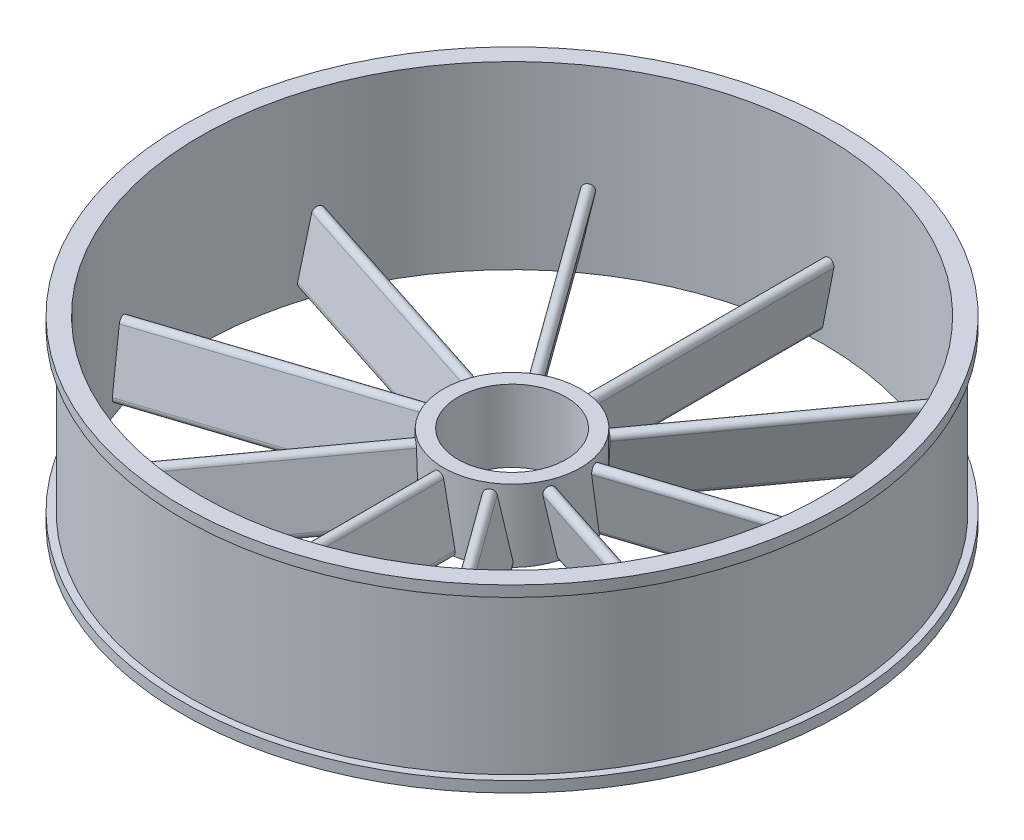
SolidWorks part; units mm, degrees
ref_plane "Plan de face" through (0, 0, 0) normal (0, 0, 1) x (1, 0, 0)
ref_plane "Plan de dessus" through (0, 0, 0) normal (0, 1, 0) x (1, 0, 0)
ref_plane "Plan de droite" through (0, 0, 0) normal (1, 0, 0) x (0, 0, -1)
sketch "Esquisse1" plane through (0, 0, 0) normal (0, 0, 1) x (1, 0, 0)
  line L0 (0, 0) -> (0, 1084.3585) construction
  line L1 (-894.2815, 25.0855) -> (-894.2815, 465.0855)
  line L2 (-864.2815, -4.9145) -> (-914.2815, -4.9145)
  line L3 (-864.2815, -4.9145) -> (-864.2815, 495.0855)
  line L4 (-864.2815, 495.0855) -> (-914.2815, 495.0855)
  line L5 (-914.2815, -4.9145) -> (-914.2815, 25.0855)
  line L6 (-894.2815, 465.0855) -> (-914.2815, 465.0855)
  line L7 (-894.2815, 25.0855) -> (-914.2815, 25.0855)
  line L8 (-914.2815, 465.0855) -> (-914.2815, 495.0855)
  dimension "D1" = 500
  dimension "D2" = 50
  dimension "D3" = 30
  dimension "D4" = 30
  dimension "D5" = 20
revolve "Révolution1" add sketch "Esquisse1" angle 360 about L0
sketch "Esquisse3" plane through (0, 0, 0) normal (0, 0, 1) x (1, 0, 0)
  line L0 (0, -352.2964) -> (0, 757.7525) construction
  line L1 (894.2815, 25.0855) -> (-894.2815, 25.0855) construction
  line L2 (-190, 25.0855) -> (-150, 25.0855)
  line L3 (-190, 25.0855) -> (-190, 225.0855)
  line L4 (-190, 225.0855) -> (-150, 225.0855)
  line L5 (-150, 25.0855) -> (-150, 225.0855)
  dimension "D1" = 200
  dimension "D2" = 40
  dimension "D3" = 150
revolve "Révolution3" add sketch "Esquisse3" angle 360 about L0
sketch "Esquisse5" plane through (0, 225.0855, 0) normal (0, 1, 0) x (1, 0, 0)
  circle A0 centre (0, 0) radius 190
  point P2 (0, 190)
ref_plane "Plan1" through (0, 225.0855, -190) normal (0, 0, -1) x (-1, 0, 0)
sketch "Esquisse7" plane through (0, 225.0855, -190) normal (0, 0, -1) x (-1, 0, 0)
  line L2 (-28.3366, -24.6437) -> (-27.3819, -29.4174)
  line L5 (2.5534, -189.2521) -> (-28.8252, -32.3592)
  line L6 (31.9708, -183.3686) -> (0.5922, -26.4757)
  arc A0 (2.5534, -189.2521) -> (31.9708, -183.3686) centre (17.2621, -186.3103) ccw
  arc A1 (0.5922, -26.4757) -> (-28.8252, -32.3592) centre (-14.1165, -29.4174) ccw
  point P8 (1.5728, -107.8639)
  dimension "D4" = 30
  dimension "D5" = 160
extrude "Boss.-Extru.1" add sketch "Esquisse7" along normal up to next contours L6 A1 L5 A0
pattern_circular "Répétition circulaire1" count 10 over 360 about axis through (0, 0, 0) along (0, 1, 0) of "Boss.-Extru.1"
